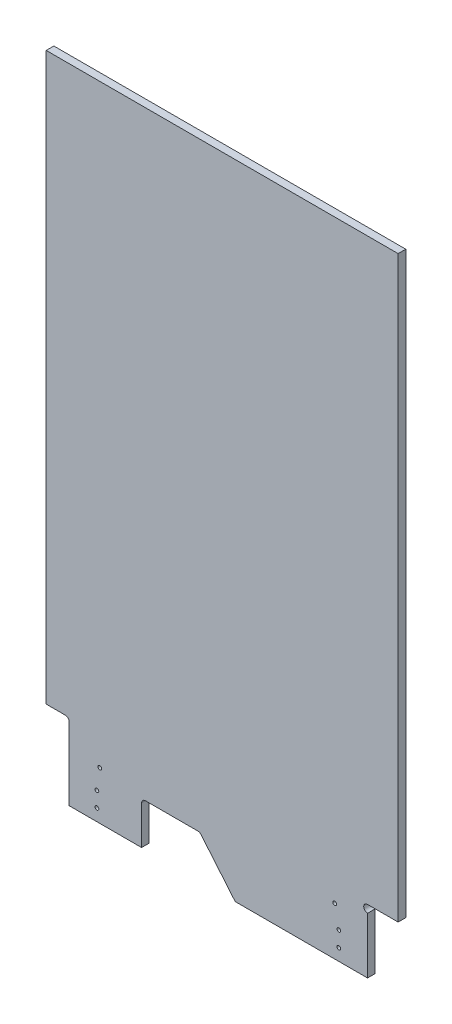
SolidWorks part; units mm, degrees
material "Maple"
ref_plane "Front Plane" through (0, 0, 0) normal (0, 0, 1) x (1, 0, 0)
ref_plane "Top Plane" through (0, 0, 0) normal (0, 1, 0) x (1, 0, 0)
ref_plane "Right Plane" through (0, 0, 0) normal (1, 0, 0) x (0, 0, -1)
sketch "Sketch1" plane through (0, 0, 0) normal (0, 0, 1) x (1, 0, 0)
  line L0 (313.7488, 0) -> (533.4, 0)
  line L1 (38.1, 0) -> (158.3263, 0)
  line L2 (584.2, 105.7904) -> (584.2, 1168.4)
  line L3 (0, 1168.4) -> (0, 127)
  line L4 (0, 1168.4) -> (584.2, 1168.4)
  line L5 (38.1, 0) -> (38.1, 120.65)
  line L6 (31.75, 127) -> (0, 127)
  line L7 (256.7734, 68.1669) -> (313.7488, 0)
  line L8 (164.6763, 70.4446) -> (251.9012, 70.4446)
  line L9 (158.3263, 0) -> (158.3263, 64.0946)
  line L10 (533.4, 93.0904) -> (533.4, 0)
  line L11 (533.4, 105.7904) -> (584.2, 105.7904)
  circle A0 centre (84.1361, 45.212) radius 3.1115
  circle A1 centre (84.1361, 19.812) radius 3.1115
  circle A2 centre (88.8986, 80.137) radius 3.1115
  arc A3 (38.1, 120.65) -> (31.75, 127) centre (31.75, 120.65) ccw
  arc A4 (256.7734, 68.1669) -> (251.9012, 70.4446) centre (251.9012, 64.0946) ccw
  arc A5 (164.6763, 70.4446) -> (158.3263, 64.0946) centre (164.6763, 64.0946) ccw
  arc A6 (533.4, 105.7904) -> (533.4, 93.0904) centre (533.4, 99.4404) ccw
  circle A7 centre (485.7736, 19.812) radius 3.1115
  circle A8 centre (478.7886, 80.137) radius 3.1115
  circle A9 centre (485.7736, 45.212) radius 3.1115
sketch "Playfield_Blank" plane through (0, 0, 0) normal (0, 0, 1) x (1, 0, 0)
  line L0 (0, 1066.8) -> (0, 0)
  line L1 (0, 0) -> (584.2, 0)
  line L2 (584.2, 0) -> (584.2, 1066.8)
  line L3 (584.2, 1066.8) -> (0, 1066.8)
  line L4 (292.1, 1066.8) -> (292.1, 0) construction
  line L5 (292.1, 533.4) -> (0, 533.4) construction
  line L6 (292.1, 533.4) -> (584.2, 533.4) construction
  dimension "Playfield_Width" = 584.2
  dimension "Playfield_Length" = 1066.8
extrude "Playfield_Thickness" add sketch "Playfield_Blank" against normal blind 12.7
sketch "Sketch3" plane through (0, 0, 0) normal (0, 0, 1) x (1, 0, 0)
  circle A0 centre (84.1361, 19.812) radius 3.1115
  circle A1 centre (84.1361, 45.212) radius 3.1115
  circle A2 centre (88.8986, 80.137) radius 3.1115
  circle A3 centre (485.7736, 19.812) radius 3.1115
  circle A4 centre (485.7736, 45.212) radius 3.1115
  circle A5 centre (478.7886, 80.137) radius 3.1115
extrude "Cut-Extrude1" cut sketch "Sketch3" against normal up to surface (12.7 mm away) up to face at (292.1, 533.4, -12.7)
sketch "Sketch4" plane through (0, 0, 0) normal (0, 0, 1) x (1, 0, 0)
  line L0 (0, 127) -> (31.75, 127)
  line L1 (38.1, 120.65) -> (38.1, 0)
  line L2 (38.1, 0) -> (0, 0)
  line L3 (0, 0) -> (0, 127)
  line L4 (0, 0) -> (584.2, 0) construction
  line L5 (0, 1066.8) -> (0, 0) construction
  arc A0 (31.75, 127) -> (38.1, 120.65) centre (31.75, 120.65) cw
  dimension "D3" = 6.35
  dimension "D1" = 127
  dimension "D2" = 38.1
extrude "Cut-Extrude2" cut sketch "Sketch4" against normal up to surface (12.7 mm away) up to face at (475.6771, 80.137, -12.7)
sketch "Sketch5" plane through (0, 0, 0) normal (0, 0, 1) x (1, 0, 0)
  line L0 (584.2, 105.791) -> (533.4, 105.791)
  line L1 (533.4, 93.091) -> (533.4, 0)
  line L2 (533.4, 0) -> (584.2, 0)
  line L3 (584.2, 0) -> (584.2, 105.791)
  line L4 (38.1, 0) -> (584.2, 0) construction
  line L5 (584.2, 0) -> (584.2, 1066.8) construction
  arc A0 (533.4, 105.791) -> (533.4, 93.091) centre (533.4, 99.441) ccw
  dimension "D3" = 6.35
  dimension "D1" = 50.8
  dimension "D2" = 105.791
  dimension "D4" = 12.7
extrude "Cut-Extrude3" cut sketch "Sketch5" against normal up to surface (12.7 mm away) up to face at (182.5236, 358.5093, -12.7)
sketch "Sketch7" plane through (0, 0, 0) normal (0, 0, 1) x (1, 0, 0)
  line L0 (158.3263, 0) -> (158.3263, 64.0946)
  line L1 (164.6763, 70.4446) -> (251.9012, 70.4446)
  line L2 (256.7734, 68.1669) -> (313.7488, 0)
  line L3 (313.7488, 0) -> (158.3263, 0)
  arc A0 (158.3263, 64.0946) -> (164.6763, 70.4446) centre (164.6763, 64.0946) cw
  arc A1 (251.9012, 70.4446) -> (256.7734, 68.1669) centre (251.9012, 64.0946) cw
extrude "Cut-Extrude4" cut sketch "Sketch7" against normal up to surface (12.7 mm away) up to face at (287.1515, 281.4238, -12.7)
